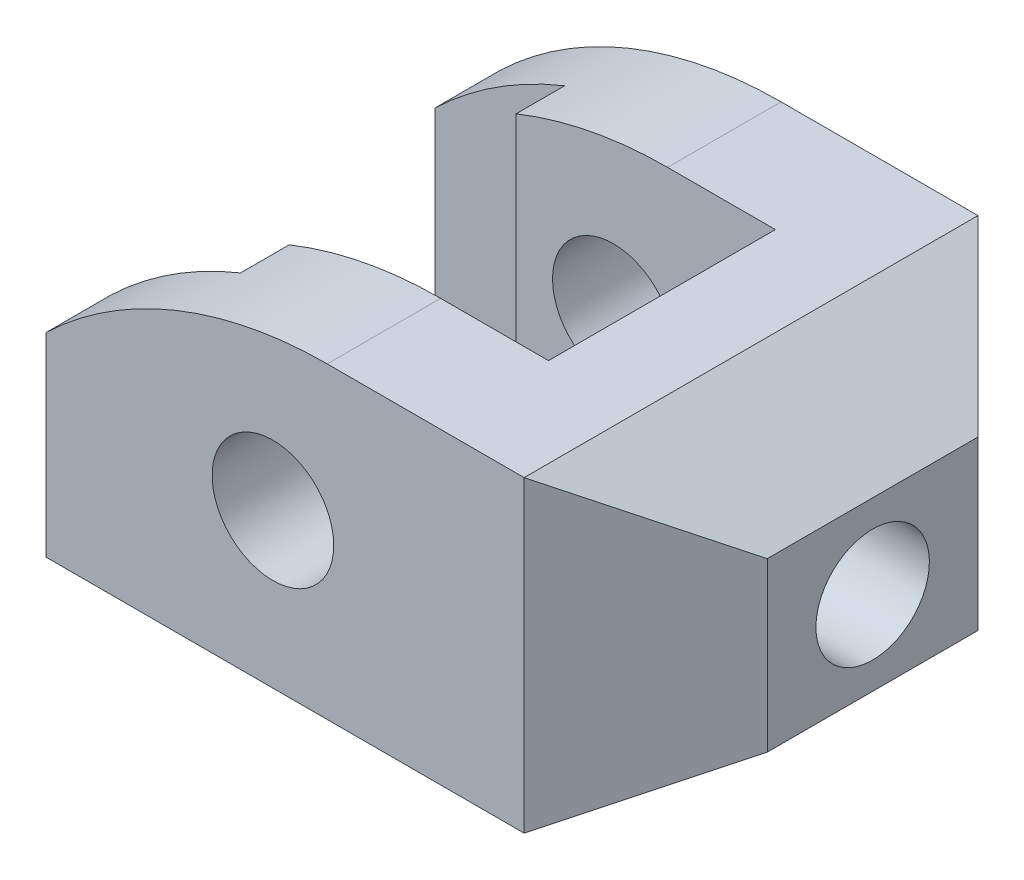
SolidWorks part; units mm, degrees
material "1060 Alloy"
ref_plane "Front Plane" through (0, 0, 0) normal (0, 0, 1) x (1, 0, 0)
ref_plane "Top Plane" through (0, 0, 0) normal (0, 1, 0) x (1, 0, 0)
ref_plane "Right Plane" through (0, 0, 0) normal (1, 0, 0) x (0, 0, -1)
sketch "Sketch1" plane through (0, 0, 0) normal (0, 0, 1) x (1, 0, 0)
  line L0 (-28, -19) -> (31, -19)
  line L1 (-28, -19) -> (-28, 5)
  line L2 (6.6987, 19) -> (31, 19)
  line L3 (0, 0) -> (0, 50000) construction
  line L4 (31, 19) -> (46, 10.3397)
  line L5 (31, -19) -> (46, -10.3397)
  line L6 (46, 10.3397) -> (46, -10.3397)
  line L7 (31, -19) -> (31, 49981) construction
  circle A0 centre (0, 0) radius 7.5
  arc A3 (6.6987, 19) -> (-28, 5) centre (6.6987, -31) ccw
  dimension "D1" = 15
  dimension "D6" = 50
  dimension "D2" = 19
  dimension "D3" = 31
  dimension "D4" = 59
  dimension "D5" = 24
  dimension "D7" = 38
  dimension "D8" = 30
  dimension "D9" = 15
  dimension "D10" = 30
extrude "Boss-Extrude1" add sketch "Sketch1" along normal blind 56
sketch "Sketch2" plane through (0, 19, 0) normal (0, 1, 0) x (1, 0, 0)
  line L0 (31, 0) -> (46, -15)
  line L1 (46, -56) -> (46, 0) construction
  line L2 (46, 0) -> (31, 0) construction
  line L3 (31, -56) -> (46, -41)
  line L4 (46, -56) -> (31, -56) construction
  line L5 (20, 0) -> (20, -56) construction
  line L6 (31, 0) -> (6.6987, 0) construction
  line L7 (31, -56) -> (6.6987, -56) construction
  line L8 (31, -56) -> (31, 0) construction
  line L9 (6.6987, -28) -> (-49993.3013, -28) construction
  line L10 (6.6987, -56) -> (6.6987, 0) construction
  line L11 (-28, 0) -> (-28, -8) construction
  line L12 (-28, -56) -> (-28, 0) construction
  line L13 (-28, -8) -> (-28, -14) construction
  line L14 (-28, -8) -> (-12, -8)
  line L15 (-12, -8) -> (-12, -14)
  line L16 (-12, -14) -> (20, -14)
  line L17 (20, -14) -> (20, -42)
  line L18 (-28, -8) -> (-28, -48)
  line L19 (-12, -42) -> (20, -42)
  line L20 (-12, -48) -> (-12, -42)
  line L21 (-28, -48) -> (-12, -48)
  line L22 (31, 0) -> (46, 0)
  line L23 (46, 0) -> (46, -15)
  line L24 (46, -41) -> (46, -56)
  line L25 (46, -56) -> (31, -56)
  point P24 (6.6987, -28)
  point P39 (20, -28)
  point P42 (-28, -28)
  dimension "D1" = 45
  dimension "D2" = 45
  dimension "D3" = 11
  dimension "D4" = 8
  dimension "D5" = 6
  dimension "D6" = 16
extrude "Cut-Extrude1" cut sketch "Sketch2" against normal up to surface (38 mm away) up to face at (1.5, -19, 28)
sketch "Sketch3" plane through (46, 0, 0) normal (1, 0, 0) x (0, 0, -1)
  line L0 (-56, -19) -> (-56, 19) construction
  line L1 (-56, -19) -> (0, -19) construction
  circle A0 centre (-28, 0) radius 7
  point P2 (-24.4457, -1.2399)
  dimension "D1" = 14
  dimension "D2" = 28
  dimension "D3" = 19
extrude "Cut-Extrude2" cut sketch "Sketch3" against normal up to surface (26 mm away) up to face at (20, 0, 28)
equation "\"A\"= 56"
equation "\"B\"= 38"
equation "\"C\"= 59"
equation "\"D4@Sketch1\"=\"C\""
equation "\"D7@Sketch1\"=\"B\""
equation "\"D1@Boss-Extrude1\"=\"A\""
equation "\"D2@Sketch3\"=\"A\"/2"
equation "\"D3@Sketch3\"=\"B\"/2"
